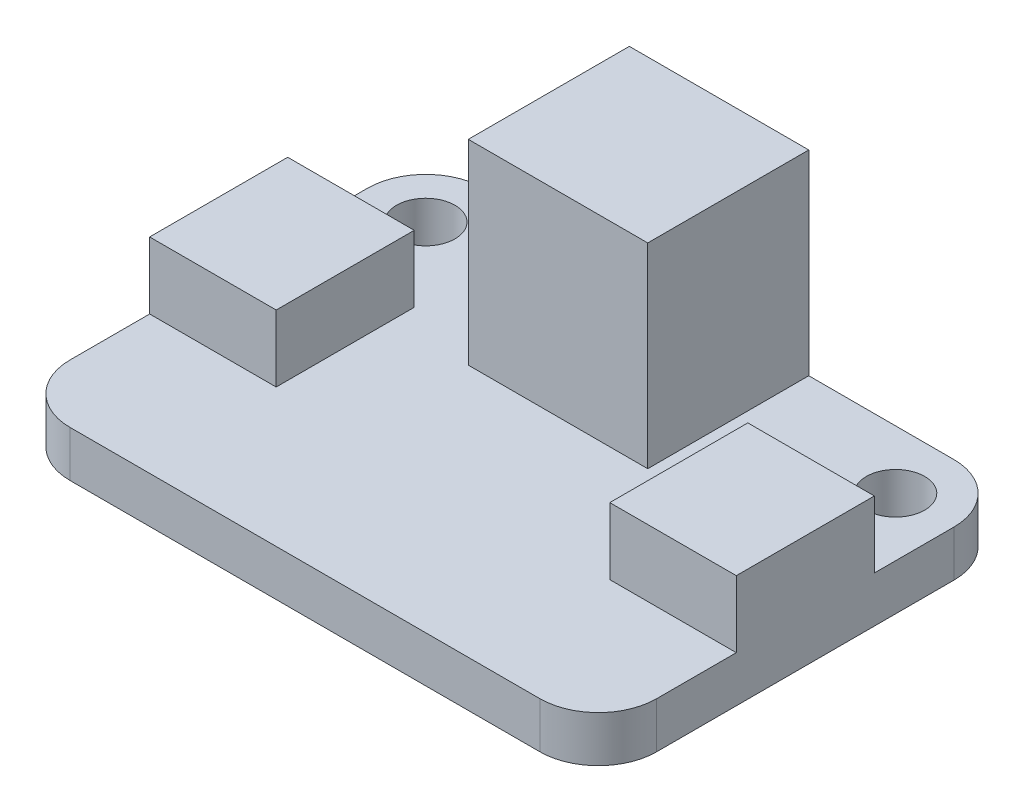
SolidWorks part; units mm, degrees
ref_plane "Front Plane" through (0, 0, 0) normal (0, 0, 1) x (1, 0, 0)
ref_plane "Top Plane" through (0, 0, 0) normal (0, 1, 0) x (1, 0, 0)
ref_plane "Right Plane" through (0, 0, 0) normal (1, 0, 0) x (0, 0, -1)
sketch "Sketch1" plane through (0, 0, 0) normal (0, 1, 0) x (1, 0, 0)
  line L1 (0, 0) -> (25.5, 0)
  line L2 (0, 0) -> (0, 18)
  line L3 (0, 18) -> (25.5, 18)
  line L4 (25.5, 0) -> (25.5, 18)
  dimension "D1" = 25.5
  dimension "D2" = 18
extrude "Boss-Extrude1" add sketch "Sketch1" along normal blind 2
sketch "Sketch2" plane through (0, 2, 0) normal (0, 1, 0) x (1, 0, 0)
  line L0 (25.5, 18) -> (0, 18) construction
  line L1 (0, 18) -> (0, 0) construction
  line L2 (12.75, 18) -> (12.75, 0) construction
  line L3 (0, 0) -> (25.5, 0) construction
  circle A0 centre (2.54, 15.46) radius 1.27
  circle A1 centre (22.96, 15.46) radius 1.27
  dimension "D1" = 2.54
  dimension "D2" = 2.54
  dimension "D3" = 2.54
extrude "Cut-Extrude1" cut sketch "Sketch2" against normal through all
sketch "Sketch3" plane through (0, 2, 0) normal (0, 1, 0) x (1, 0, 0)
  line L0 (12.75, 18) -> (12.75, 0) construction
  line L1 (25.5, 18) -> (0, 18) construction
  line L2 (0, 0) -> (25.5, 0) construction
  line L3 (0, 18) -> (0, 0) construction
  line L4 (0, 12) -> (5.5, 12)
  line L5 (0, 12) -> (0, 6)
  line L6 (0, 6) -> (5.5, 6)
  line L7 (5.5, 12) -> (5.5, 6)
  line L8 (25.5, 9) -> (0, 9) construction
  line L9 (25.5, 0) -> (25.5, 18) construction
  line L10 (25.5, 6) -> (20, 6)
  line L11 (20, 12) -> (20, 6)
  line L12 (25.5, 12) -> (20, 12)
  line L13 (25.5, 12) -> (25.5, 6)
  point P16 (0, 0)
  point P17 (0, 9)
  dimension "D1" = 6
  dimension "D2" = 5.5
extrude "Boss-Extrude2" add sketch "Sketch3" along normal blind 2.9
sketch "Sketch4" plane through (0, 2, 0) normal (0, 1, 0) x (1, 0, 0)
  line L0 (12.75, 18) -> (12.75, 0) construction
  line L1 (25.5, 18) -> (0, 18) construction
  line L2 (0, 0) -> (25.5, 0) construction
  line L4 (8.85, 18) -> (16.65, 18)
  line L5 (8.85, 18) -> (8.85, 11)
  line L6 (8.85, 11) -> (16.65, 11)
  line L7 (16.65, 18) -> (16.65, 11)
  point P10 (12.75, 18)
  dimension "D1" = 7.8
  dimension "D2" = 7
extrude "Boss-Extrude3" add sketch "Sketch4" along normal blind 8.5
fillet "Fillet1" radius 2.54 4 edges at (25.5, 1, 0) (25.5, 1, -18) (0, 1, -18) (0, 1, 0)
